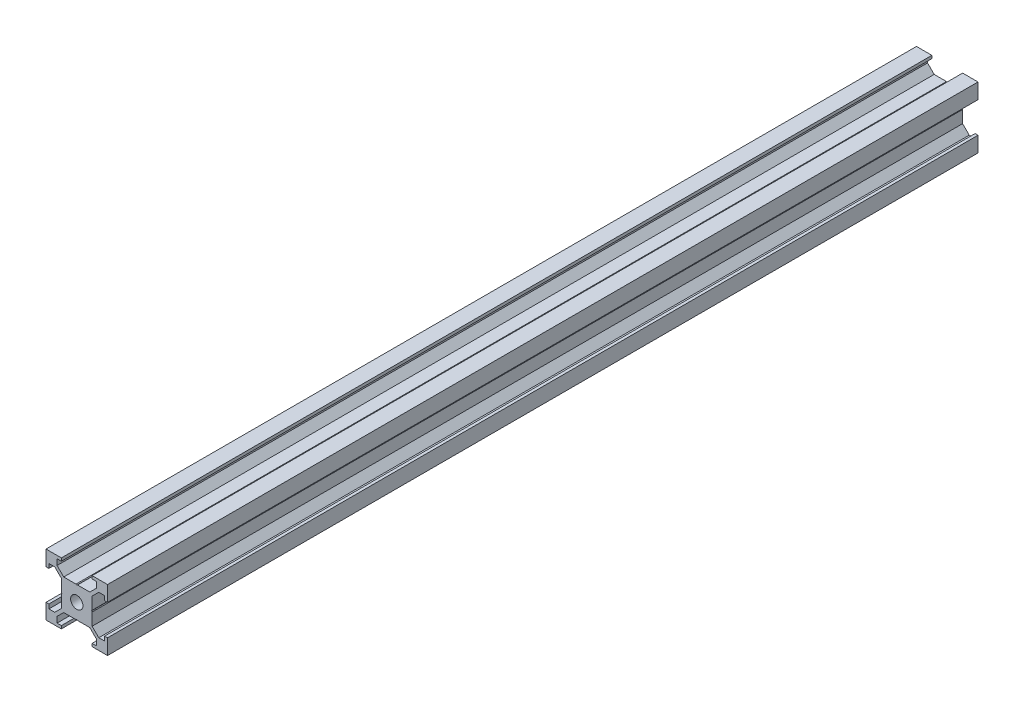
SolidWorks part; units mm, degrees
material "5052-H38"
ref_plane "Front Plane" through (0, 0, 0) normal (0, 0, 1) x (1, 0, 0)
ref_plane "Top Plane" through (0, 0, 0) normal (0, 1, 0) x (1, 0, 0)
ref_plane "Right Plane" through (0, 0, 0) normal (1, 0, 0) x (0, 0, -1)
sketch "Sketch1" plane through (0, 0, 0) normal (0, 0, 1) x (1, 0, 0)
  line L0 (-10, 5) -> (-9.0563, 5)
  line L1 (10, -10) -> (5, -10)
  line L2 (10, -10) -> (10, -5)
  line L3 (10, 10) -> (5, 10)
  line L4 (-10, -10) -> (-10, -5)
  line L5 (10, -10) -> (-10, 10) construction
  line L6 (10, 10) -> (-10, -10) construction
  line L7 (5, -5) -> (0.2457, -5)
  line L8 (5, -5) -> (5, -0.2457)
  line L9 (5, 5) -> (0.2457, 5)
  line L10 (-5, -5) -> (-5, -0.2457)
  line L11 (5, -5) -> (-5, 5) construction
  line L12 (5, 5) -> (-5, -5) construction
  line L13 (-9.0563, 5) -> (-9.0563, 6.4)
  line L14 (-9.0563, 6.4) -> (-7.1563, 6.4)
  line L15 (-7.1563, 6.4) -> (-5, 4.2437)
  line L16 (-5, 10) -> (-5, 9.0563)
  line L17 (-5, 9.0563) -> (-6.4, 9.0563)
  line L18 (-6.4, 9.0563) -> (-6.4, 7.1563)
  line L19 (-6.4, 7.1563) -> (-4.2437, 5)
  line L20 (5, 10) -> (5, 9.0563)
  line L21 (5, 9.0563) -> (6.4, 9.0563)
  line L22 (6.4, 9.0563) -> (6.4, 7.1563)
  line L23 (6.4, 7.1563) -> (4.2437, 5)
  line L24 (7.1563, 6.4) -> (5, 4.2437)
  line L25 (9.0563, 6.4) -> (7.1563, 6.4)
  line L26 (10, 5) -> (9.0563, 5)
  line L27 (9.0563, 5) -> (9.0563, 6.4)
  line L28 (10, -5) -> (9.0563, -5)
  line L29 (9.0563, -5) -> (9.0563, -6.4)
  line L30 (9.0563, -6.4) -> (7.1563, -6.4)
  line L31 (7.1563, -6.4) -> (5, -4.2437)
  line L32 (6.4, -7.1563) -> (4.2437, -5)
  line L33 (6.4, -9.0563) -> (6.4, -7.1563)
  line L34 (5, -10) -> (5, -9.0563)
  line L35 (5, -9.0563) -> (6.4, -9.0563)
  line L36 (-5, -10) -> (-5, -9.0563)
  line L37 (-5, -9.0563) -> (-6.4, -9.0563)
  line L38 (-6.4, -9.0563) -> (-6.4, -7.1563)
  line L39 (-6.4, -7.1563) -> (-4.2437, -5)
  line L40 (-7.1563, -6.4) -> (-5, -4.2437)
  line L41 (-9.0563, -6.4) -> (-7.1563, -6.4)
  line L42 (-10, -5) -> (-9.0563, -5)
  line L43 (-9.0563, -5) -> (-9.0563, -6.4)
  line L44 (0, 0) -> (-5, 0) construction
  line L45 (-5, 0.2457) -> (-4.8279, 0)
  line L46 (-4.8279, 0) -> (-5, -0.2457)
  line L47 (0.2457, 5) -> (0, 4.8279)
  line L48 (0, 4.8279) -> (-0.2457, 5)
  line L49 (5, -0.2457) -> (4.8279, 0)
  line L50 (4.8279, 0) -> (5, 0.2457)
  line L51 (-0.2457, -5) -> (0, -4.8279)
  line L52 (0, -4.8279) -> (0.2457, -5)
  line L53 (-0.2457, 5) -> (-5, 5)
  line L54 (5, 0.2457) -> (5, 5)
  line L55 (-0.2457, -5) -> (-5, -5)
  line L56 (-5, 0.2457) -> (-5, 5)
  line L57 (-10, 5) -> (-10, 10)
  line L58 (-5, 10) -> (-10, 10)
  line L59 (-5, -10) -> (-10, -10)
  line L60 (10, 5) -> (10, 10)
  circle A0 centre (0, 0) radius 2
  point P0 (0, 0)
  point P6 (0, 0)
  point P56 (0, 0)
  point P70 (0, 0)
  dimension "D10" = 4
  dimension "D1" = 20
  dimension "D2" = 10
  dimension "D3" = 1.4
  dimension "D4" = 1.9
  dimension "D5" = 3.0494
  dimension "D7" = 0.3
  dimension "D8" = 35
  dimension "D6" = 4
  dimension "D9" = 4
extrude "Boss-Extrude1" add sketch "Sketch1" along normal blind 283 contours L26 L60 L3 L20 L21 L22 L23 L9 L54 L24 L25 L27 | L56 L45 L46 L10 L55 L51 L52 L7 L8 L49 L50 L54 L9 L47 L48 L53 A0 | L16 L58 L57 L0 L13 L14 L15 L56 L53 L19 L18 L17 | L59 L36 L37 L38 L39 L55 L10 L40 L41 L43 L42 L4 | L35 L34 L1 L2 L28 L29 L30 L31 L8 L7 L32 L33
